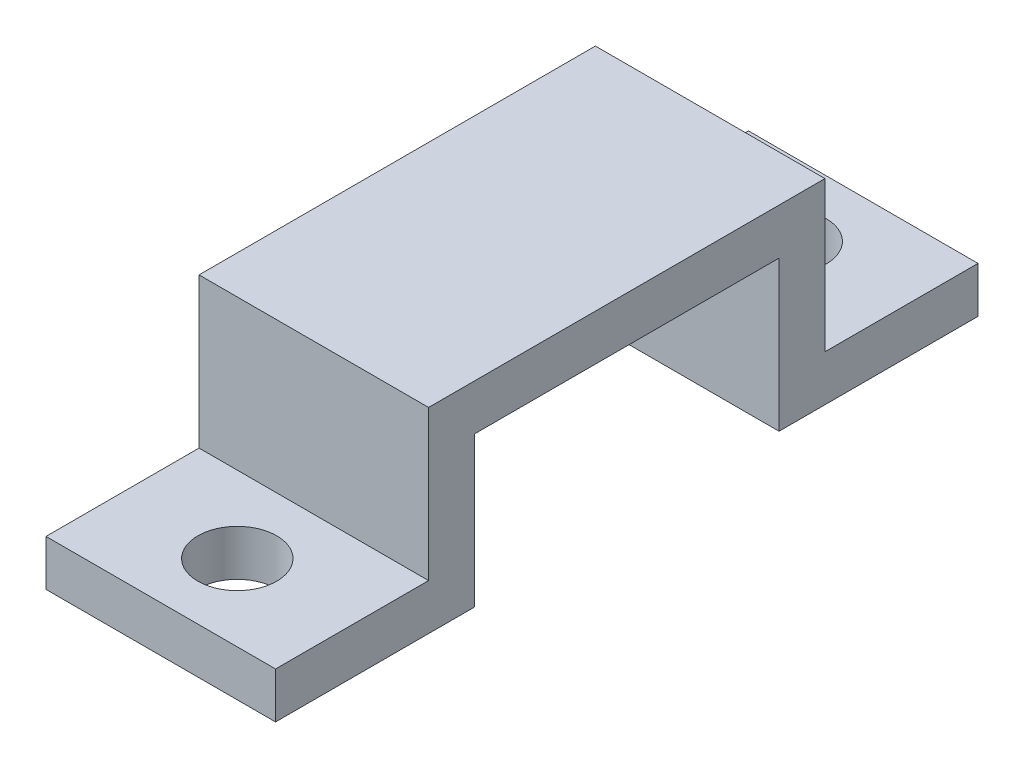
SolidWorks part; units mm, degrees
ref_plane "Alzado" through (0, 0, 0) normal (0, 0, 1) x (1, 0, 0)
ref_plane "Planta" through (0, 0, 0) normal (0, 1, 0) x (1, 0, 0)
ref_plane "Vista lateral" through (0, 0, 0) normal (1, 0, 0) x (0, 0, -1)
sketch "Croquis2" plane through (0, 0, 0) normal (1, 0, 0) x (0, 0, -1)
  line L0 (-22.95, -12.8) -> (-9.95, -12.8)
  line L1 (-9.95, -12.8) -> (-9.95, -3)
  line L2 (-9.95, -3) -> (9.95, -3)
  line L4 (12.95, 0) -> (-12.95, 0)
  line L5 (-12.95, 0) -> (-12.95, -9.8)
  line L6 (-12.95, -9.8) -> (-22.95, -9.8)
  line L7 (-22.95, -9.8) -> (-22.95, -12.8)
  line L8 (0, 0) -> (0, -18.0411) construction
  line L9 (22.95, -9.8) -> (22.95, -12.8)
  line L10 (12.95, -9.8) -> (22.95, -9.8)
  line L11 (22.95, -12.8) -> (9.95, -12.8)
  line L12 (9.95, -12.8) -> (9.95, -3)
  line L13 (12.95, 0) -> (12.95, -9.8)
  dimension "D1" = 3
  dimension "D2" = 19.9
  dimension "D3" = 3
  dimension "D4" = 3
  dimension "D5" = 10
  dimension "D6" = 9.8
extrude "Saliente-Extruir1" add sketch "Croquis2" along normal blind 15
sketch "Croquis5" plane through (0, -9.8, 0) normal (0, 1, 0) x (1, 0, 0)
  line L0 (0, -22.95) -> (15, -12.95) construction
  circle A0 centre (7.5, -17.95) radius 2.575
  dimension "D1" = 5.15
extrude "Cortar-Extruir1" cut sketch "Croquis5" against normal through all
mirror "Simetría1" about plane through (0, 0, 0) normal (0, 0, 1) of "Cortar-Extruir1"
